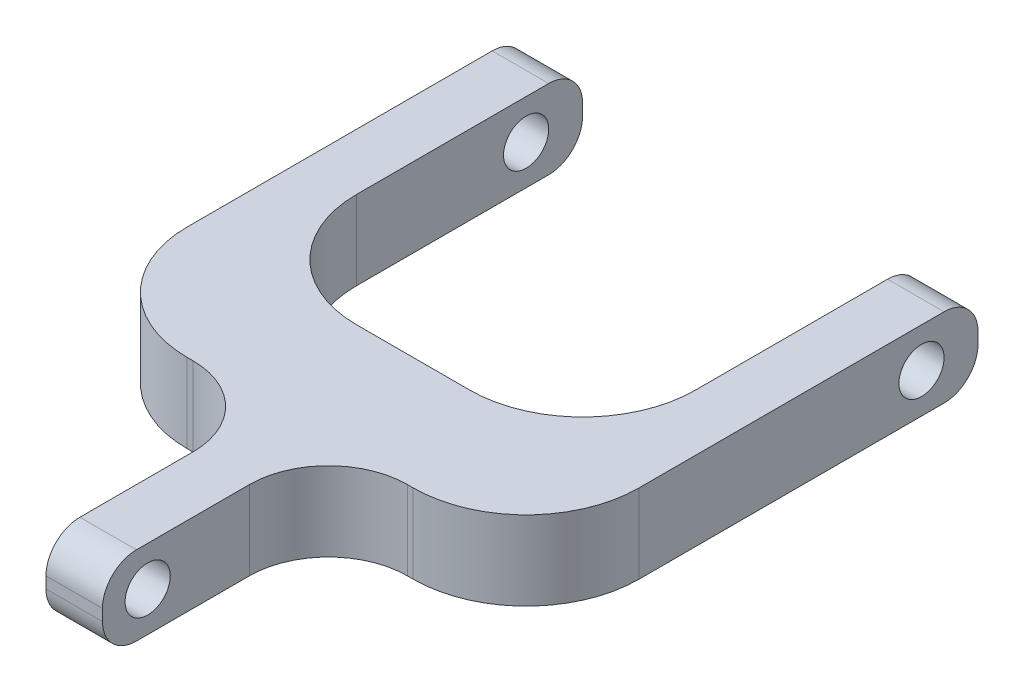
SolidWorks part; units mm, degrees
ref_plane "Front Plane" through (0, 0, 0) normal (0, 0, 1) x (1, 0, 0)
ref_plane "Top Plane" through (0, 0, 0) normal (0, 1, 0) x (1, 0, 0)
ref_plane "Right Plane" through (0, 0, 0) normal (1, 0, 0) x (0, 0, -1)
sketch "Sketch1" plane through (0, 0, 0) normal (1, 0, 0) x (0, 0, -1)
  line L1 (-20, 3.5) -> (20, 3.5)
  line L2 (-20, 3.5) -> (-20, -3.5)
  line L3 (-20, -3.5) -> (20, -3.5)
  line L4 (20, 3.5) -> (20, -3.5)
  line L5 (-20, 3.5) -> (20, -3.5) construction
  line L6 (-20, -3.5) -> (20, 3.5) construction
  point P0 (0, 0)
  dimension "D1" = 7
  dimension "D2" = 40
extrude "Boss-Extrude1" add sketch "Sketch1" along normal blind 40
sketch "Sketch2" plane through (0, 3.5, 0) normal (0, 1, 0) x (1, 0, 0)
  line L0 (40, 20) -> (0, 20) construction
  line L1 (5, 20) -> (35, 20)
  line L2 (5, 20) -> (5, 0)
  line L3 (15, -10) -> (25, -10)
  line L4 (35, 20) -> (35, 0)
  line L5 (0, 20) -> (0, -20) construction
  line L6 (40, 20) -> (40, -20) construction
  arc A0 (25, -10) -> (35, 0) centre (25, 0) ccw
  arc A1 (5, 0) -> (15, -10) centre (15, 0) ccw
  point P14 (5, -10)
  dimension "D4" = 10
  dimension "D1" = 5
  dimension "D2" = 5
  dimension "D3" = 30
extrude "Cut-Extrude1" cut sketch "Sketch2" against normal through all
fillet "Fillet1" radius 10 2 edges at (40, 0, 20) (0, 0, 20)
sketch "Sketch5" plane through (0, 0, 20) normal (0, 0, 1) x (1, 0, 0)
  line L0 (30, 3.5) -> (10, 3.5) construction
  line L1 (17.5, 3.5) -> (22.5, 3.5)
  line L2 (17.5, 3.5) -> (17.5, -3.5)
  line L3 (17.5, -3.5) -> (22.5, -3.5)
  line L4 (22.5, 3.5) -> (22.5, -3.5)
  line L5 (30, -3.5) -> (10, -3.5) construction
  line L6 (20, 3.5) -> (20, -3.5) construction
  point P10 (20, -3.5)
  dimension "D1" = 5
extrude "Boss-Extrude2" add sketch "Sketch5" along normal blind 20
fillet "Fillet2" radius 7 2 edges at (22.5, 0, 20) (17.5, 0, 20)
fillet "Fillet3" radius 3 6 edges at (2.5, -3.5, -20) (2.5, 3.5, -20) (37.5, -3.5, -20) (37.5, 3.5, -20) (20, -3.5, 40) (20, 3.5, 40)
sketch "Sketch6" plane through (40, 0, 0) normal (1, 0, 0) x (0, 0, -1)
  line L0 (15, 0) -> (0, 0) construction
  circle A0 centre (15, 0) radius 2
  dimension "D1" = 15
extrude "Cut-Extrude2" cut sketch "Sketch6" against normal through all
sketch "Sketch7" plane through (22.5, 0, 0) normal (1, 0, 0) x (0, 0, -1)
  line L0 (0, 0) -> (-36, 0) construction
  circle A0 centre (-36, 0) radius 2
  dimension "D1" = 36
extrude "Cut-Extrude3" cut sketch "Sketch7" against normal through all
